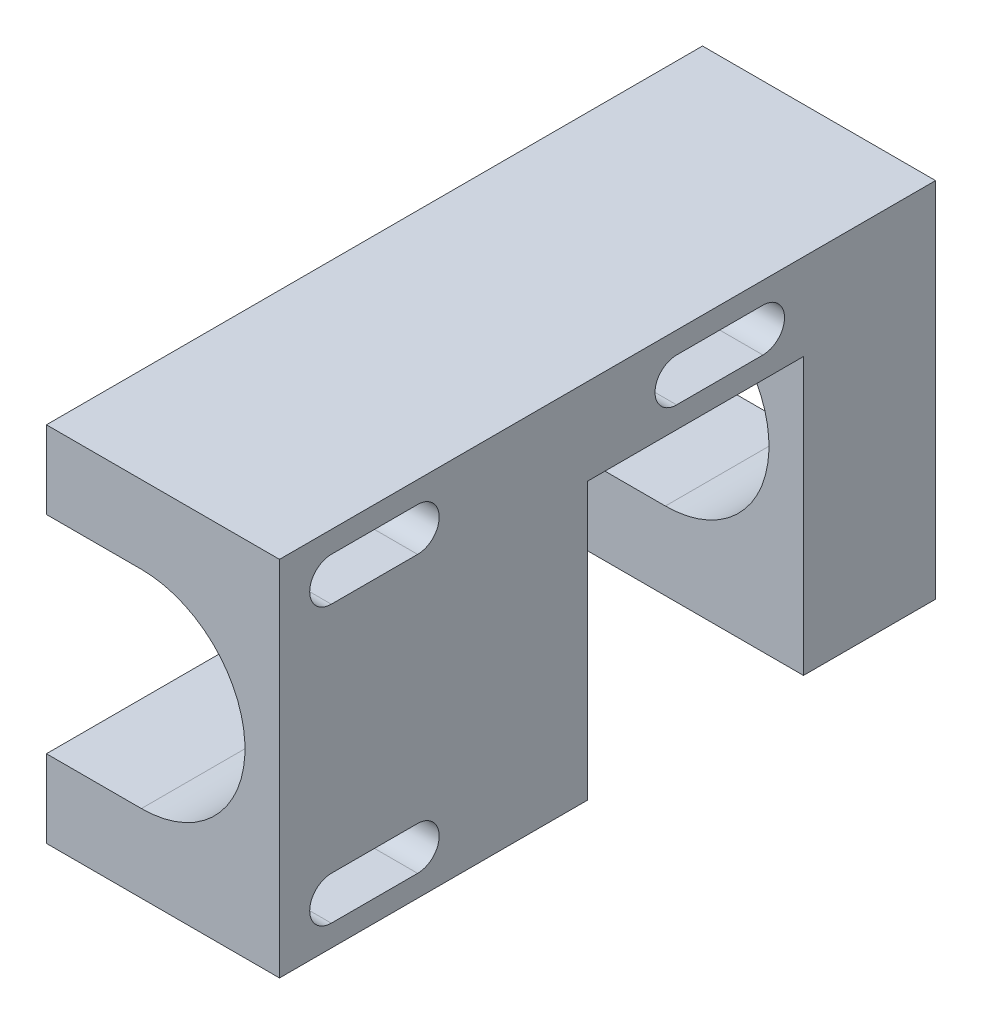
SolidWorks part; units mm, degrees
ref_plane "Front Plane" through (0, 0, 0) normal (0, 0, 1) x (1, 0, 0)
ref_plane "Top Plane" through (0, 0, 0) normal (0, 1, 0) x (1, 0, 0)
ref_plane "Right Plane" through (0, 0, 0) normal (1, 0, 0) x (0, 0, -1)
sketch "Sketch2" plane through (0, 0, 0) normal (0, 0, 1) x (1, 0, 0)
  line L0 (0, 0) -> (0, 42)
  line L1 (0, 42) -> (27, 42)
  line L2 (27, 42) -> (27, 0)
  line L3 (27, 0) -> (0, 0)
  dimension "D1" = 27
  dimension "D2" = 42
extrude "Boss-Extrude1" add sketch "Sketch2" against normal blind 76
sketch "Sketch3" plane through (0, 0, 0) normal (-1, 0, 0) x (0, 0, 1)
  line L0 (-56, 39.5) -> (-46, 39.5)
  line L1 (-56, 34.5) -> (-46, 34.5)
  line L2 (-16, 39.5) -> (-6, 39.5)
  line L3 (-16, 34.5) -> (-6, 34.5)
  line L4 (-16, 7.5) -> (-6, 7.5)
  line L5 (-16, 2.5) -> (-6, 2.5)
  line L6 (-76, 42) -> (0, 42) construction
  line L7 (-76, 0) -> (0, 0) construction
  line L8 (0, 42) -> (0, 0) construction
  line L9 (-76, 42) -> (-76, 0) construction
  arc A3 (-56, 39.5) -> (-56, 34.5) centre (-56, 37) ccw
  arc A4 (-46, 34.5) -> (-46, 39.5) centre (-46, 37) ccw
  arc A5 (-16, 39.5) -> (-16, 34.5) centre (-16, 37) ccw
  arc A6 (-6, 34.5) -> (-6, 39.5) centre (-6, 37) ccw
  arc A7 (-16, 7.5) -> (-16, 2.5) centre (-16, 5) ccw
  arc A8 (-6, 2.5) -> (-6, 7.5) centre (-6, 5) ccw
  dimension "D2" = 10
  dimension "D4" = 5
  dimension "D5" = 5
  dimension "D6" = 5
  dimension "D7" = 5
  dimension "D8" = 6
  dimension "D9" = 20
  dimension "D10" = 2.5
  dimension "D11" = 2.5
  dimension "D13" = 2.5
  dimension "D14" = 2.5
  dimension "D15" = 6
  dimension "D16" = 5
  dimension "D1" = 5
  dimension "D3" = 10
  dimension "D12" = 10
extrude "Cut-Extrude1" cut sketch "Sketch3" against normal through all
sketch "Sketch4" plane through (0, 0, 0) normal (0, 0, 1) x (1, 0, 0)
  line L0 (27, 0) -> (27, 42) construction
  line L2 (11, 33) -> (0, 33)
  line L3 (0, 42) -> (0, 0) construction
  line L4 (0, 33) -> (0, 9)
  line L5 (0, 9) -> (11, 9)
  line L6 (0, 0) -> (27, 0) construction
  arc A0 (11, 33) -> (11, 9) centre (11, 21) cw
  dimension "D1" = 12
  dimension "D2" = 16
  dimension "D3" = 21
  dimension "D4" = 9
extrude "Cut-Extrude2" cut sketch "Sketch4" against normal through all
sketch "Sketch5" plane through (27, 0, 0) normal (1, 0, 0) x (0, 0, -1)
  line L0 (35.7, 0) -> (35.7, 32)
  line L1 (76, 0) -> (0, 0) construction
  line L2 (35.7, 32) -> (60.7, 32)
  line L3 (60.7, 32) -> (60.7, 0)
  line L4 (60.7, 0) -> (35.7, 0)
  line L5 (76, 0) -> (76, 42) construction
  dimension "D1" = 25
  dimension "D2" = 32
  dimension "D3" = 15.3
extrude "Cut-Extrude3" cut sketch "Sketch5" against normal through all
